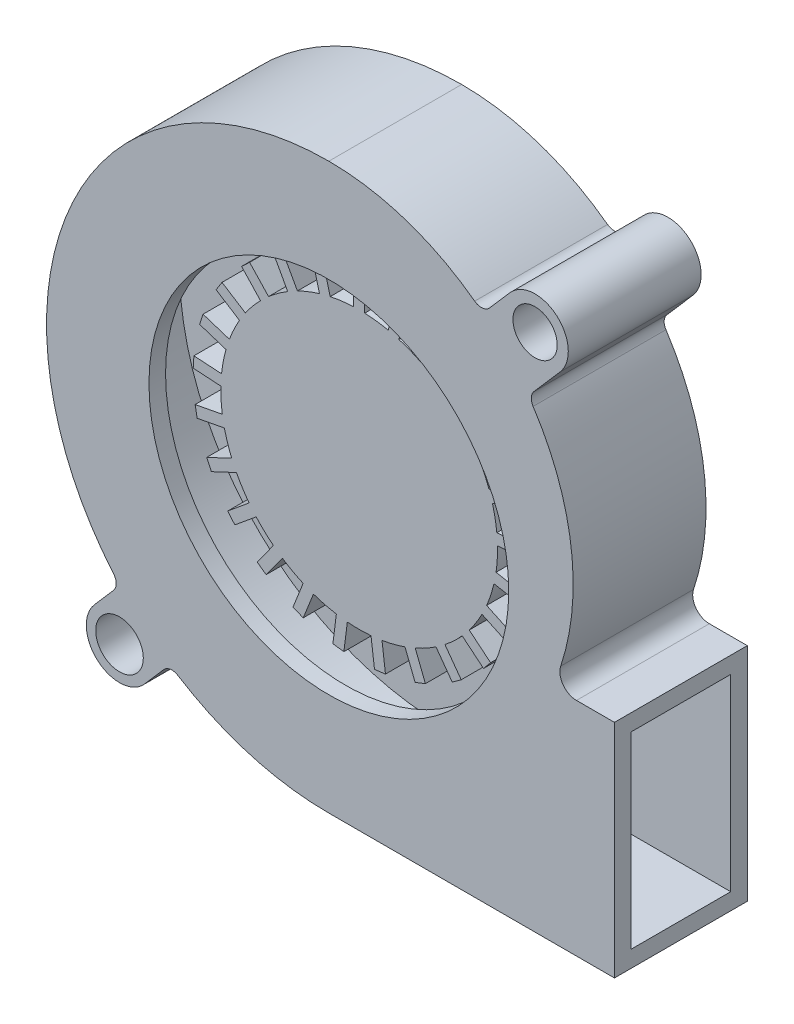
SolidWorks part; units mm, degrees
material "ABS"
ref_plane "Front Plane" through (0, 0, 0) normal (0, 0, 1) x (1, 0, 0)
ref_plane "Top Plane" through (0, 0, 0) normal (0, 1, 0) x (1, 0, 0)
ref_plane "Right Plane" through (0, 0, 0) normal (1, 0, 0) x (0, 0, -1)
sketch "Sketch1" plane through (0, 0, 0) normal (0, 0, 1) x (1, 0, 0)
  line L0 (0, -25.5) -> (25.8, -25.5)
  line L1 (25.8, -25.5) -> (25.8, -5.5)
  line L2 (25.8, -5.5) -> (24.8998, -5.5)
  arc A0 (24.8998, -5.5) -> (0, -25.5) centre (0, 0) ccw
  point P1 (-25.5, 0)
  point P6 (0, 25.5)
  dimension "D1" = 51.3
  dimension "D2" = 51
  dimension "D3" = 20
extrude "Boss-Extrude1" add sketch "Sketch1" along normal blind 12
sketch "Sketch5" plane through (0, 0, 12) normal (0, 0, 1) x (1, 0, 0)
  line L0 (24.8998, -5.5) -> (20.1827, -5.5)
  arc A0 (20.1827, -5.5) -> (0, 25.5) centre (0, 3.43) ccw
  arc A1 (24.8998, -5.5) -> (0, -25.5) centre (0, 0) ccw construction
  arc A2 (24.8998, -5.5) -> (0, 25.5) centre (0, 0) ccw
  dimension "D1" = 44.14
extrude "Cut-Extrude2" cut sketch "Sketch5" against normal blind 28.5
shell "Shell1" thickness 1.5
sketch "Sketch2" plane through (0, 0, 12) normal (0, 0, 1) x (1, 0, 0)
  circle A0 centre (0, 0) radius 16.25
  dimension "D1" = 32.5
extrude "Cut-Extrude1" cut sketch "Sketch2" against normal blind 3.76
sketch "Sketch3" plane through (0, 0, 1.5) normal (0, 0, 1) x (1, 0, 0)
  circle A0 centre (0, 0) radius 12.5
  dimension "D1" = 25
extrude "Boss-Extrude2" add sketch "Sketch3" along normal blind 7.76
sketch "Sketch4" plane through (0, 0, 1.5) normal (0, 0, 1) x (1, 0, 0)
  line L0 (-0.5, 12.49) -> (-0.5, 14.99)
  line L1 (-0.5, 14.99) -> (0.5, 14.99)
  line L2 (0.5, 14.99) -> (0.5, 12.49)
  circle A0 centre (0, 0) radius 12.5 construction
  arc A1 (-0.5, 12.49) -> (0.5, 12.49) centre (0, 0) cw
  point P4 (0, 14.99)
  dimension "D1" = 1
  dimension "D2" = 2.5
extrude "Boss-Extrude3" add sketch "Sketch4" along normal blind 7.76
pattern_circular "CirPattern1" count 25 over 360 about axis through (0, 0, 0) along (0, 0, 1) of "Boss-Extrude3"
fillet "Fillet1" radius 1.5 1 edges at (20.1827, -5.5, 6)
sketch "Sketch6" plane through (0, 0, 12) normal (0, 0, 1) x (1, 0, 0)
  line L0 (-18.8775, -17.1433) -> (-21.1737, -19.7848)
  line L1 (-16.6454, -23.7211) -> (-14.3492, -21.0796)
  line L2 (-16.6454, -23.7211) -> (-21.1737, -19.7848) construction
  line L3 (-20.8777, -24.0171) -> (0, 0) construction
  line L4 (0, -25.5) -> (25.8, -25.5) construction
  arc A0 (0, 25.5) -> (0, -25.5) centre (0, 0) ccw construction
  arc A1 (-21.1737, -19.7848) -> (-16.6454, -23.7211) centre (-18.9095, -21.7529) ccw
  arc A2 (-18.8775, -17.1433) -> (-14.3492, -21.0796) centre (0, 0) ccw
  circle A3 centre (-18.9095, -21.7529) radius 2.15
  dimension "D3" = 3
  dimension "D4" = 4.3
  dimension "D1" = 3.5
  dimension "D2" = 49
extrude "Boss-Extrude4" add sketch "Sketch6" against normal up to surface (12 mm away) up to face at (12.7222, -5.839, 0)
fillet "Fillet2" radius 1 2 edges at (-18.8775, -17.1433, 6) (-14.3492, -21.0796, 6)
sketch "Sketch7" plane through (0, 0, 12) normal (0, 0, 1) x (1, 0, 0)
  line L0 (13.905, 20.5687) -> (16.3653, 23.3988)
  line L1 (20.8935, 19.4625) -> (18.026, 16.1638)
  line L2 (16.3653, 23.3988) -> (20.8935, 19.4625) construction
  line L3 (-18.9095, -21.7529) -> (35.1748, 40.464) construction
  arc A0 (20.9448, -3.5272) -> (0, 25.5) centre (0, 3.43) ccw construction
  arc A1 (16.3653, 23.3988) -> (20.8935, 19.4625) centre (18.6294, 21.4307) cw
  circle A4 centre (18.6294, 21.4307) radius 2
  arc A5 (18.026, 16.1638) -> (13.905, 20.5687) centre (0, 3.43) ccw
  dimension "D2" = 3
  dimension "D3" = 4
  dimension "D1" = 3.75
extrude "Boss-Extrude5" add sketch "Sketch7" against normal up to surface (12 mm away) up to face at (-1.5746, -12.7427, 0)
fillet "Fillet3" radius 1 2 edges at (13.905, 20.5687, 6) (18.026, 16.1638, 6)
